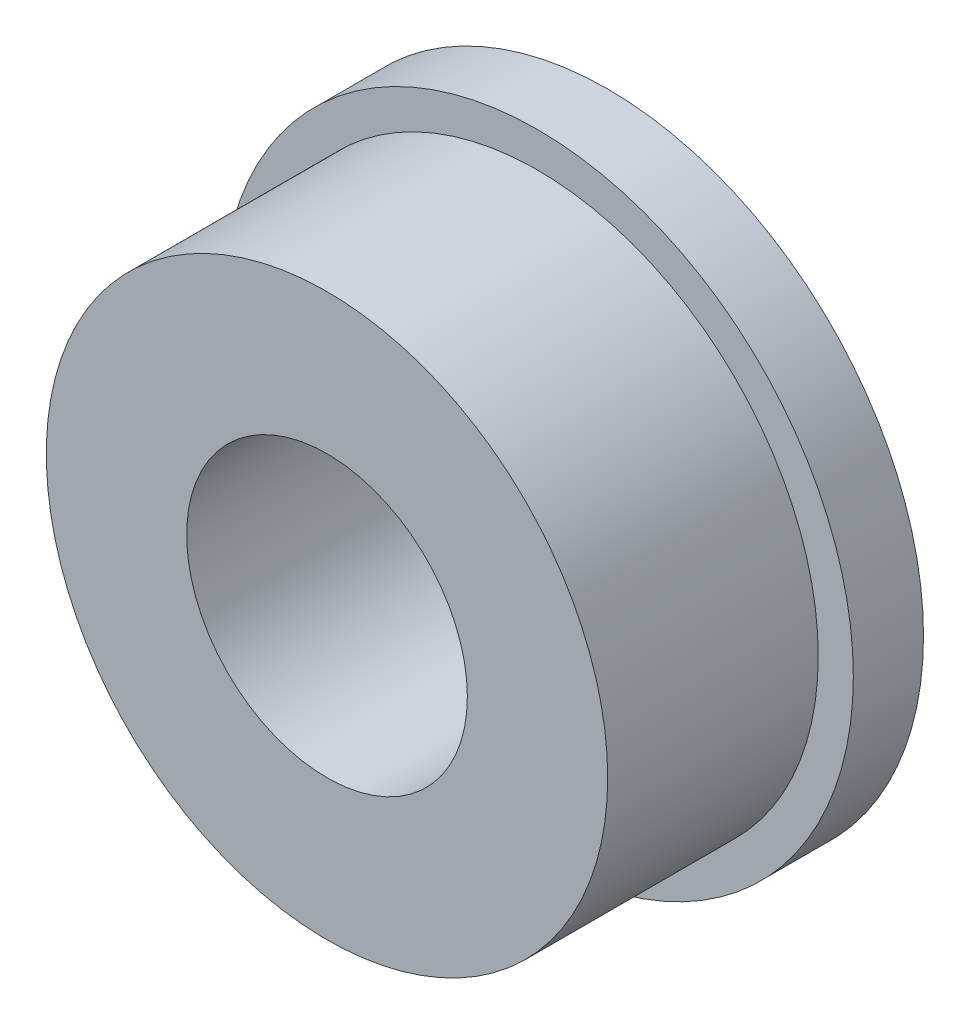
SolidWorks part; units mm, degrees
ref_plane "前视基准面" through (0, 0, 0) normal (0, 0, 1) x (1, 0, 0)
ref_plane "上视基准面" through (0, 0, 0) normal (0, 1, 0) x (1, 0, 0)
ref_plane "右视基准面" through (0, 0, 0) normal (1, 0, 0) x (0, 0, -1)
sketch "草图1" plane through (0, 0, 0) normal (0, 0, 1) x (1, 0, 0)
  circle A0 centre (0, 0) radius 9
  circle A1 centre (0, 0) radius 4
  dimension "D1" = 8
  dimension "D2" = 18
extrude "凸台-拉伸1" add sketch "草图1" along normal blind 2
sketch "草图2" plane through (0, 0, 2) normal (0, 0, 1) x (1, 0, 0)
  circle A0 centre (0, 0) radius 8
  circle A1 centre (0, 0) radius 4
  dimension "D1" = 16
extrude "凸台-拉伸2" add sketch "草图2" along normal blind 6
